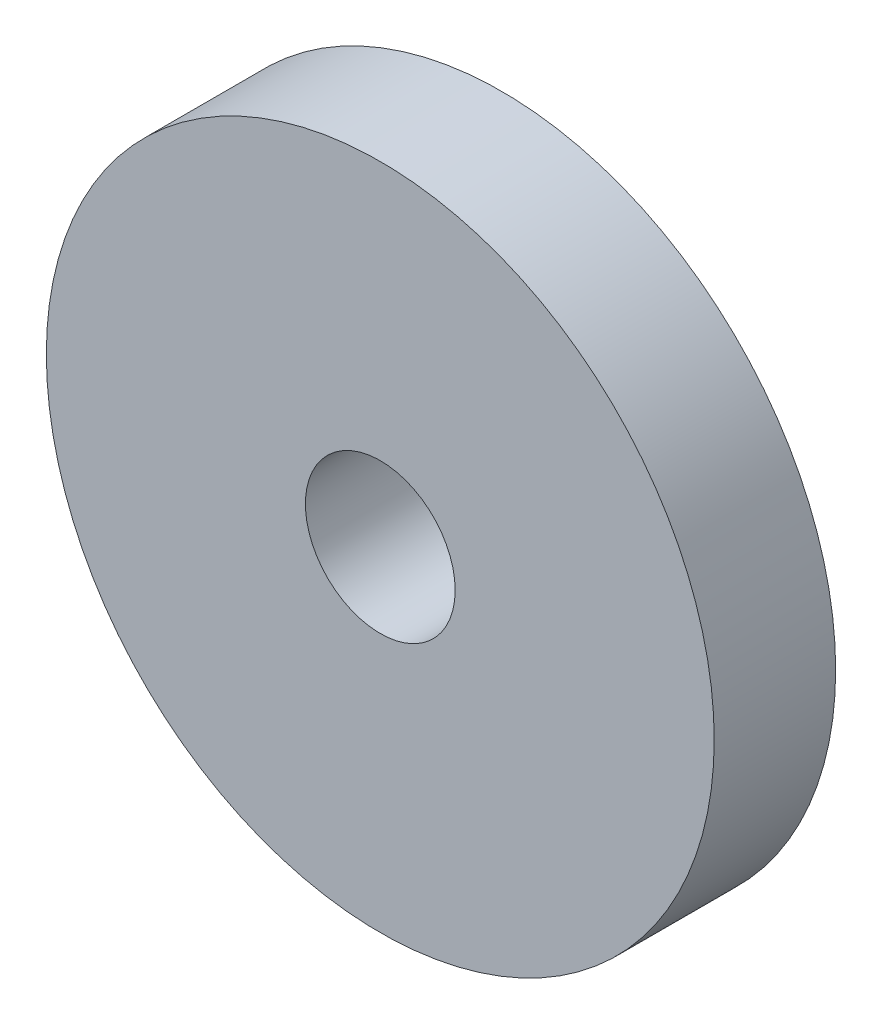
SolidWorks part; units mm, degrees
ref_plane "Ebene vorne" through (0, 0, 0) normal (0, 0, 1) x (1, 0, 0)
ref_plane "Ebene oben" through (0, 0, 0) normal (0, 1, 0) x (1, 0, 0)
ref_plane "Ebene rechts" through (0, 0, 0) normal (1, 0, 0) x (0, 0, -1)
sketch "Skizze1" plane through (0, 0, 0) normal (0, 0, 1) x (1, 0, 0)
  circle A0 centre (0, 0) radius 8.25
  circle A1 centre (0, 0) radius 1.85
  dimension "D1" = 16.5
  dimension "D2" = 3.7
extrude "Aufsatz-Linear austragen1" add sketch "Skizze1" along normal blind 3
